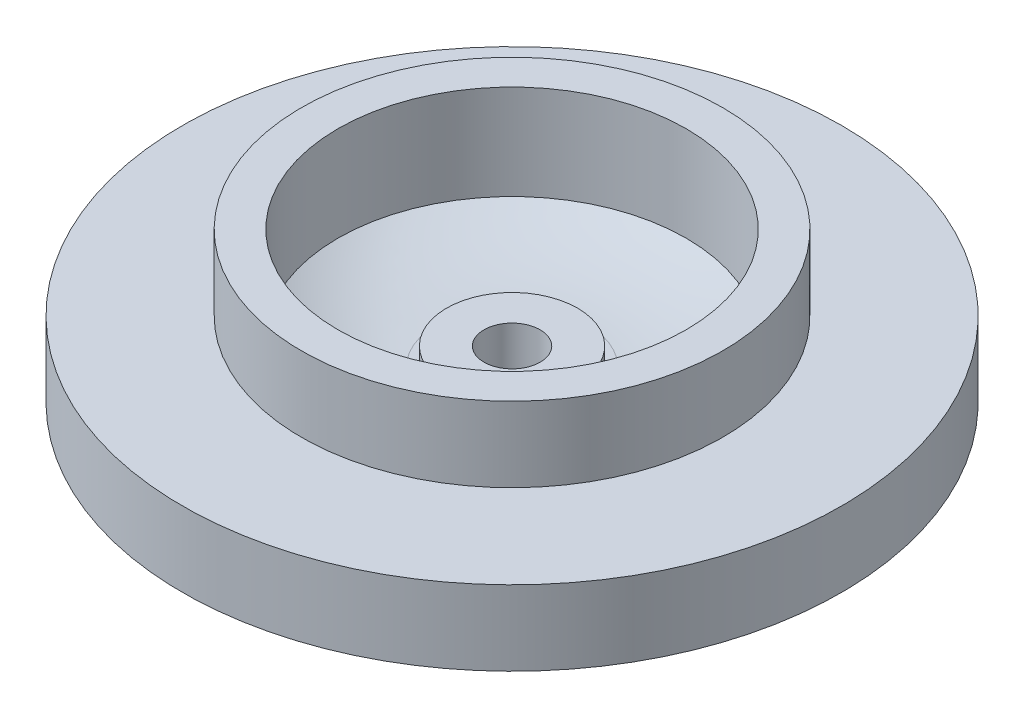
SolidWorks part; units mm, degrees
ref_plane "Front Plane" through (0, 0, 0) normal (0, 0, 1) x (1, 0, 0)
ref_plane "Top Plane" through (0, 0, 0) normal (0, 1, 0) x (1, 0, 0)
ref_plane "Right Plane" through (0, 0, 0) normal (1, 0, 0) x (0, 0, -1)
sketch "Sketch1" plane through (0, 0, 0) normal (0, 0, 1) x (1, 0, 0)
  line L0 (0, 0) -> (0, 26.0954) construction
  line L1 (-17.6, 1.5) -> (-17.6, 5.5)
  line L2 (-17.6, 5.5) -> (-11.25, 5.5)
  line L3 (-11.25, 5.5) -> (-11.25, 9.5)
  line L4 (-11.25, 9.5) -> (-9.3, 9.5)
  line L5 (-9.3, 9.5) -> (-9.3, 4.4359)
  line L6 (-17.6, 1.5) -> (-16.6, 1.5)
  line L7 (-16.6, 1.5) -> (-16.6, 3)
  line L8 (-16.6, 3) -> (-13.5, 3)
  line L9 (-13.5, 3) -> (-13.5, 0)
  line L10 (-13.5, 0) -> (-8.75, 0)
  line L11 (-8.75, 0) -> (-8.75, 3.5)
  line L12 (-4, 2.5) -> (-0.8806, 2.5) construction
  line L13 (-4, 2.5) -> (-4, 0)
  line L14 (-4, 0) -> (0, 0)
  line L15 (-4, 3.1) -> (-3.5, 3.1)
  line L16 (0, 4.1) -> (0, 0)
  line L17 (-3.5, 3.1) -> (-3.5, 4.1)
  line L18 (-3.5, 4.1) -> (0, 4.1)
  arc A0 (-4, 2.5) -> (-8.75, 3.5) centre (-4, 14.2813) cw
  arc A1 (-4, 3.1) -> (-9.3, 4.4359) centre (-4, 14.2813) cw
  arc A2 (-4, 3.1) -> (-8.5081, 4.0491) centre (-4, 14.2813) cw construction
  dimension "D1" = 35.2
  dimension "D2" = 1.5
  dimension "D3" = 1.5
  dimension "D4" = 1
  dimension "D5" = 27
  dimension "D6" = 17.5
  dimension "D7" = 8
  dimension "D8" = 3.5
  dimension "D9" = 2.5
  dimension "D11" = 18.6
  dimension "D12" = 22.5
  dimension "D13" = 5.5
  dimension "D14" = 9.5
  dimension "D15" = 7
  dimension "D16" = 1
  dimension "D10" = 0.6
revolve "Revolve1" add sketch "Sketch1" angle 360 about L0
sketch "Sketch2" plane through (0, 4.1, 0) normal (0, 1, 0) x (1, 0, 0)
  circle A0 centre (0, 0) radius 1.5
  dimension "D1" = 3
extrude "Cut-Extrude1" cut sketch "Sketch2" against normal blind 10
